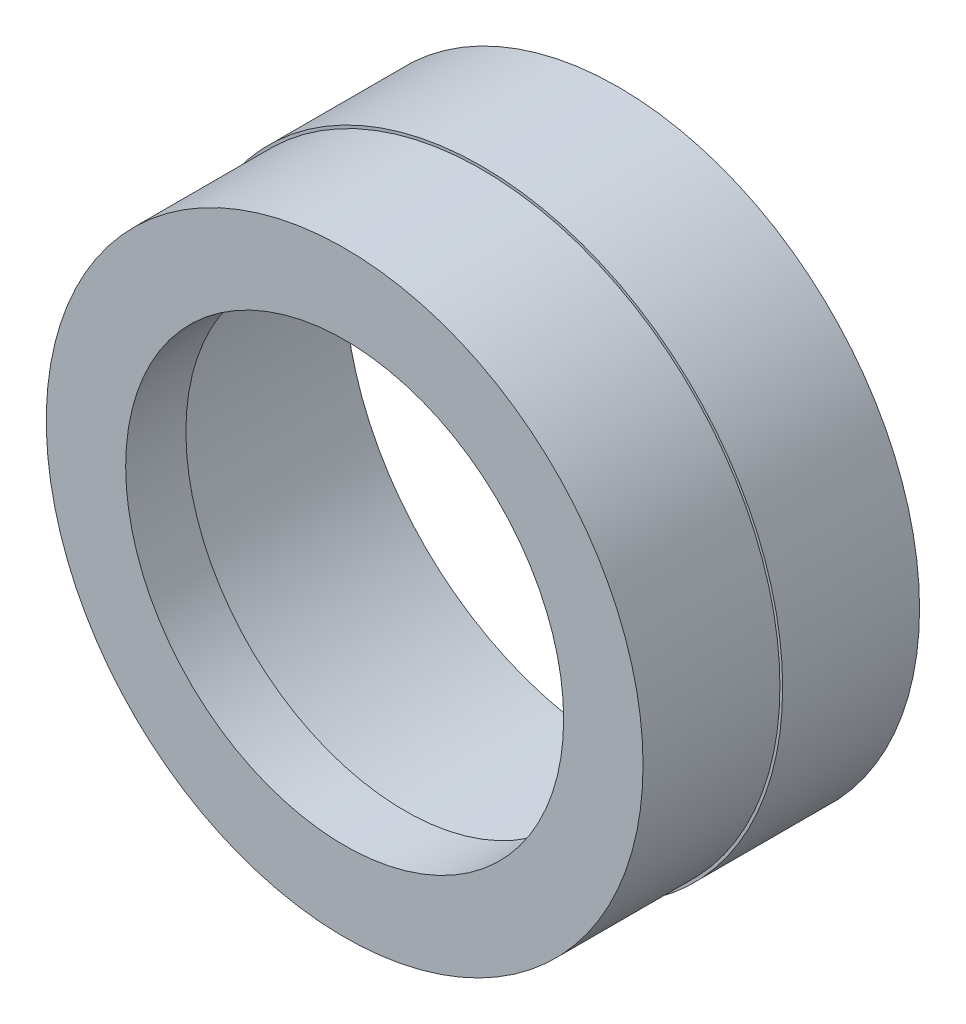
SolidWorks part; units mm, degrees
ref_plane "Front Plane" through (0, 0, 0) normal (0, 0, 1) x (1, 0, 0)
ref_plane "Top Plane" through (0, 0, 0) normal (0, 1, 0) x (1, 0, 0)
ref_plane "Right Plane" through (0, 0, 0) normal (1, 0, 0) x (0, 0, -1)
sketch "Sketch1" plane through (0, 0, 0) normal (0, 0, 1) x (1, 0, 0)
  circle A0 centre (0, 0) radius 5.5
  dimension "D1" = 11
extrude "Boss-Extrude1" add sketch "Sketch1" against normal blind 5
sketch "Sketch2" plane through (0, 0, -5) normal (0, 0, -1) x (-1, 0, 0)
  circle A0 centre (0, 0) radius 5
  dimension "D1" = 10
extrude "Cut-Extrude1" cut sketch "Sketch2" against normal blind 3.9
sketch "Sketch3" plane through (0, 0, 0) normal (0, 0, 1) x (1, 0, 0)
  circle A0 centre (0, 0) radius 4
  dimension "D1" = 8
extrude "Cut-Extrude2" cut sketch "Sketch3" against normal up to next
sketch "Sketch4" plane through (0, 0, 0) normal (0, 0, 1) x (1, 0, 0)
  circle A0 centre (0, 0) radius 5.45
  dimension "D1" = 10.9
extrude "Cut-Extrude3" cut sketch "Sketch4" against normal blind 2.5 flip side to cut
